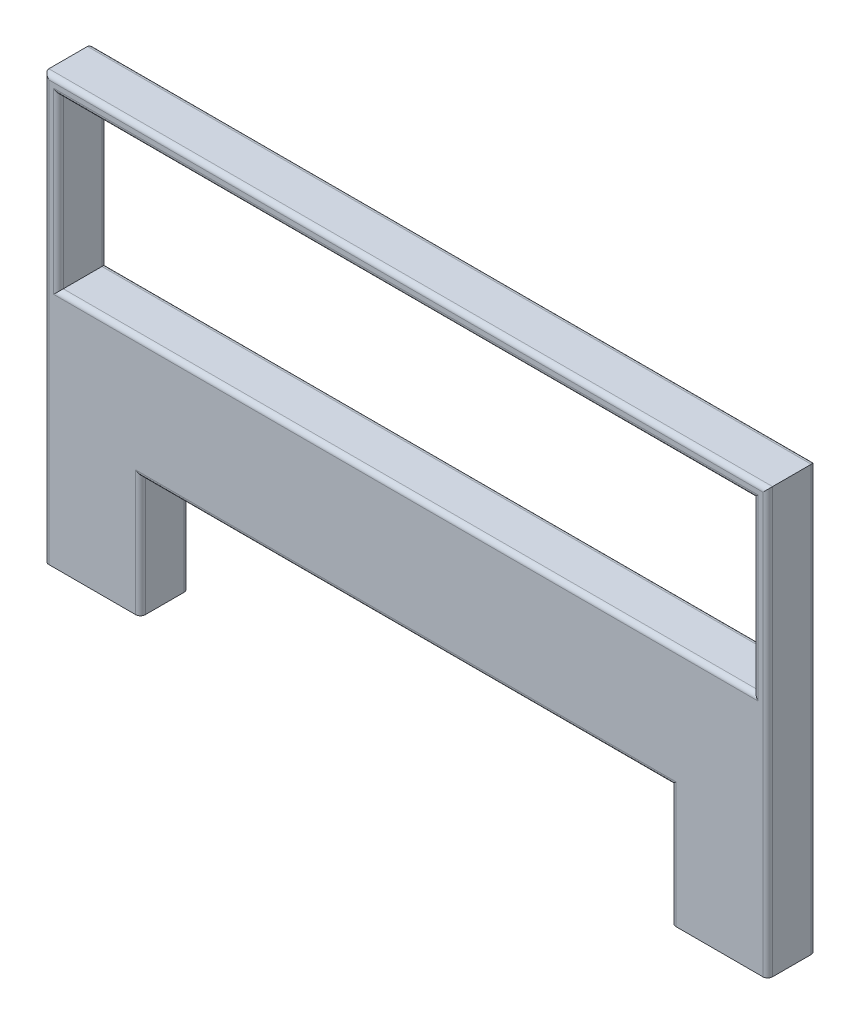
SolidWorks part; units mm, degrees
material "Cedar"
ref_plane "Front Plane" through (0, 0, 0) normal (0, 0, 1) x (1, 0, 0)
ref_plane "Top Plane" through (0, 0, 0) normal (0, 1, 0) x (1, 0, 0)
ref_plane "Right Plane" through (0, 0, 0) normal (1, 0, 0) x (0, 0, -1)
sketch "Sketch1" plane through (0, 0, 0) normal (0, 0, 1) x (1, 0, 0)
  line L0 (-840.3361, 0) -> (599.6639, 0)
  line L2 (629.6639, -500) -> (429.6639, -500)
  line L3 (429.6639, -500) -> (429.6639, -250)
  line L4 (429.6639, -250) -> (-670.3361, -250)
  line L5 (-670.3361, -250) -> (-670.3361, -500)
  line L6 (-670.3361, -500) -> (-870.3361, -500)
  line L8 (629.6639, 380) -> (629.6639, -500)
  line L9 (-870.3361, 380) -> (629.6639, 380)
  line L11 (-840.3361, 350) -> (599.6639, 350)
  line L16 (-840.3361, 350) -> (-840.3361, 0)
  line L20 (599.6639, 350) -> (599.6639, 0)
  line L21 (-870.3361, 380) -> (-870.3361, -500)
  point P0 (529.6639, -500)
  dimension "D1" = 30
  dimension "D2" = 200
  dimension "D3" = 200
  dimension "D4" = 1500
  dimension "D5" = 350
  dimension "D6" = 250
  dimension "D7" = 250
  dimension "D8" = 30
  dimension "D9" = 30
  dimension "D10" = 30
extrude "Boss-Extrude1" add sketch "Sketch1" along normal blind 100
fillet "Fillet1" radius 10 20 edges at (-120.3361, -250, 100) (-120.3361, 350, 100) (-120.3361, -250, 0) (-120.3361, 350, 0) (-840.3361, 175, 0) (599.6639, 175, 0) (-840.3361, 175, 100) (599.6639, 175, 100) (-120.3361, 0, 0) (-120.3361, 0, 100) (429.6639, -375, 0) (-670.3361, -375, 0) (429.6639, -375, 100) (-670.3361, -375, 100) (-870.3361, -60, 0) (-870.3361, -60, 100) (-120.3361, 380, 100) (-120.3361, 380, 0) (629.6639, -60, 0) (629.6639, -60, 100)
